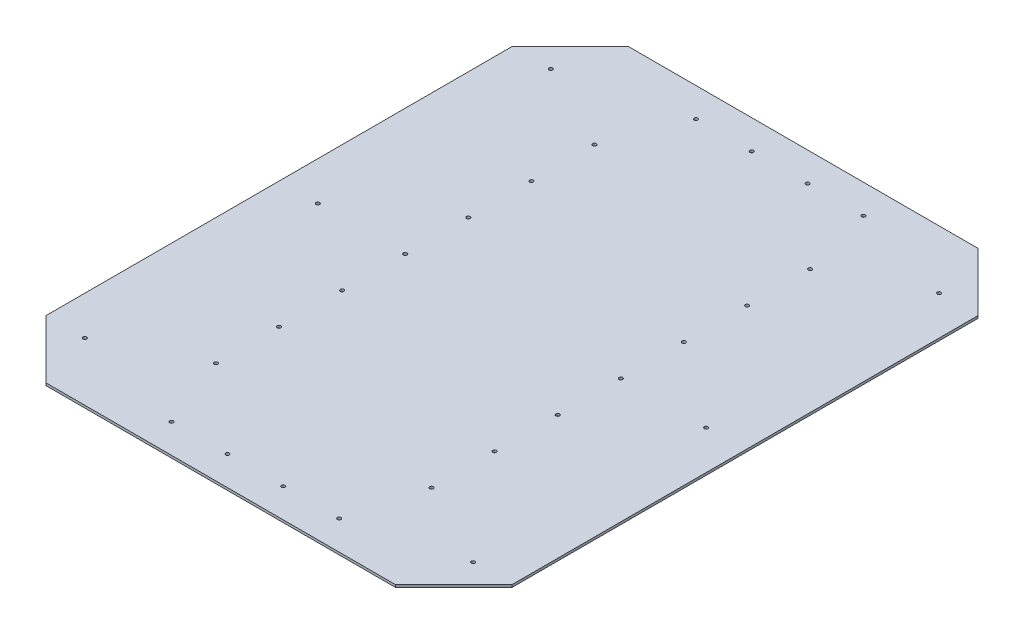
SolidWorks part; units mm, degrees
material "AISI 1010 Steel, hot rolled bar"
ref_plane "Front Plane" through (0, 0, 0) normal (0, 0, 1) x (1, 0, 0)
ref_plane "Top Plane" through (0, 0, 0) normal (0, 1, 0) x (1, 0, 0)
ref_plane "Right Plane" through (0, 0, 0) normal (1, 0, 0) x (0, 0, -1)
sketch "Sketch1" plane through (0, 0, 0) normal (0, 1, 0) x (1, 0, 0)
  line L1 (-609.6, 762) -> (609.6, 762)
  line L2 (-609.6, 762) -> (-609.6, -762)
  line L3 (-609.6, -762) -> (609.6, -762)
  line L4 (609.6, 762) -> (609.6, -762)
  line L5 (-609.6, 762) -> (609.6, -762) construction
  line L6 (-609.6, -762) -> (609.6, 762) construction
  point P0 (0, 0)
  dimension "D1" = 1219.2
  dimension "D2" = 1524
extrude "Boss-Extrude1" add sketch "Sketch1" along normal blind 6.35
sketch "Sketch2" plane through (0, 0, 0) normal (0, -1, 0) x (1, 0, 0)
  line L0 (-609.6, 762) -> (-609.6, 685.8) construction
  line L1 (-609.6, 762) -> (609.6, 762) construction
  line L2 (-609.6, -762) -> (-609.6, 762) construction
  line L3 (-609.6, -762) -> (-609.6, -685.8) construction
  line L4 (-609.6, -685.8) -> (609.6, -685.8) construction
  line L5 (609.6, 762) -> (609.6, -762) construction
  line L6 (-609.6, 685.8) -> (609.6, 685.8) construction
  line L7 (-609.6, 0) -> (609.6, 0) construction
  dimension "D1" = 76.2
sketch "Sketch12" plane through (-609.6, 0, 0) normal (-1, 0, 0) x (0, 0, 1)
  line L0 (-533.4, 0) -> (-533.4, -50.8)
  line L1 (-762, 0) -> (-685.8, 0) construction
  line L2 (533.4, 0) -> (533.4, -50.8)
  line L3 (762, 0) -> (685.8, 0) construction
  line L4 (0, 0) -> (0, -50.8)
  line L5 (-762, 0) -> (762, 0) construction
  dimension "D1" = 50.8
  dimension "D2" = 50.8
ref_plane "Plane2" through (0, -50.8, 0) normal (0, -1, 0) x (-1, 0, 0)
sketch "Sketch14" plane through (0, -50.8, 0) normal (0, -1, 0) x (-1, 0, 0)
  line L0 (609.6, 685.8) -> (-609.6, 685.8) construction
  line L1 (609.6, -685.8) -> (-609.6, -685.8) construction
  line L2 (609.6, 685.8) -> (-609.6, 685.8)
  line L3 (609.6, -685.8) -> (-609.6, -685.8)
  line L4 (609.6, 0) -> (-609.6, 0)
sketch "Sketch20" plane through (0, 6.35, 0) normal (0, 1, 0) x (1, 0, 0)
  line L0 (0, -762) -> (0, 762) construction
  line L1 (-609.6, -762) -> (609.6, -762) construction
  line L2 (609.6, 762) -> (-609.6, 762) construction
  line L3 (-457.2, 762) -> (0, 762)
  line L4 (0, 762) -> (457.2, 762)
  line L5 (457.2, 762) -> (609.6, 609.6)
  line L6 (609.6, -762) -> (609.6, 762) construction
  line L7 (-457.2, 762) -> (-609.6, 609.6)
  line L8 (-609.6, 762) -> (-609.6, -762) construction
  line L9 (-609.6, 0) -> (609.6, 0) construction
  line L10 (-457.2, -762) -> (-609.6, -609.6)
  line L11 (457.2, -762) -> (609.6, -609.6)
  line L12 (0, -762) -> (457.2, -762)
  line L13 (-457.2, -762) -> (0, -762)
  line L14 (-609.6, -609.6) -> (-609.6, 609.6)
  line L15 (609.6, 609.6) -> (609.6, -609.6)
  line L16 (609.6, 609.6) -> (609.6, -609.6)
  circle A0 centre (0, 0) radius 1360.3436
  dimension "D1" = 457.2
  dimension "D2" = 45
  dimension "D3" = 45
  dimension "D4" = 45
  dimension "D5" = 457.2
extrude "Cut-Extrude-Thin2" cut sketch "Sketch20" against normal up to surface (6.35 mm away) thin contours A0 | L5 L4 L3 L7 L14 L10 L13 L12 L11 up to face at (0, 0, 0) thin type one direction wall 2.54
other "Structural Member1" [suppressed]
ref_plane "Plane3" through (-609.6, -50.8, -685.8) normal (1, 0, 0) x (0, -1, 0)
sketch "Sketch13" plane through (-609.6, -50.8, -685.8) normal (1, 0, 0) x (0, -1, 0)
  line L0 (-44.45, -69.85) -> (-44.45, 69.85)
  line L1 (44.45, 69.85) -> (-44.45, 69.85)
  line L2 (44.45, 69.85) -> (44.45, -69.85)
  line L3 (-44.45, -69.85) -> (44.45, -69.85)
  line L4 (-50.8, -76.2) -> (50.8, -76.2)
  line L5 (-50.8, -76.2) -> (-50.8, 76.2)
  line L6 (50.8, 76.2) -> (-50.8, 76.2)
  line L7 (50.8, 76.2) -> (50.8, -76.2)
  line L8 (0, 76.2) -> (0, 69.85) construction
  line L9 (0, 69.85) -> (0, -69.85) construction
  line L10 (0, -69.85) -> (0, -76.2) construction
  line L11 (50.8, 0) -> (44.45, 0) construction
  line L12 (44.45, 0) -> (-44.45, 0) construction
  line L13 (-44.45, 0) -> (-50.8, 0) construction
  point P16 (0, 0)
  dimension "Thickness" = 6.35
  dimension "V_leg" = 152.4
  dimension "H_leg" = 101.6
sketch "Sketch16" [suppressed] plane through (0, -101.6, 0) normal (0, -1, 0) x (1, 0, 0)
  line L0 (-762, 0) -> (-685.8, 0) construction
  line L1 (-762, 76.2) -> (-762, -76.2) construction
  line L2 (-762, 762) -> (-762, 609.6) construction
  line L3 (-762, 685.8) -> (-685.8, 685.8) construction
  line L4 (-762, -685.8) -> (-685.8, -685.8) construction
  line L5 (-762, -609.6) -> (-762, -762) construction
  line L6 (762, -685.8) -> (685.8, -685.8) construction
  line L7 (762, -609.6) -> (762, -762) construction
  line L8 (762, 0) -> (685.8, 0) construction
  line L9 (762, 76.2) -> (762, -76.2) construction
  line L10 (762, 685.8) -> (685.8, 685.8) construction
  line L11 (762, 762) -> (762, 609.6) construction
  line L12 (762, 685.8) -> (-762, 685.8) construction
  line L13 (762, -685.8) -> (-762, -685.8) construction
  line L14 (0, -685.8) -> (0, -609.6) construction
  line L15 (762, -609.6) -> (-762, -609.6) construction
  line L16 (0, 685.8) -> (0, 762) construction
  line L17 (762, 762) -> (-762, 762) construction
  circle A0 centre (685.8, 685.8) radius 12.7
  circle A1 centre (685.8, 0) radius 12.7
  circle A2 centre (685.8, -685.8) radius 12.7
  circle A3 centre (-685.8, -685.8) radius 12.7
  circle A4 centre (-685.8, 0) radius 12.7
  circle A5 centre (-685.8, 685.8) radius 12.7
  circle A6 centre (0, 685.8) radius 12.7
  circle A7 centre (0, -685.8) radius 12.7
  dimension "D2" = 25.4
  dimension "D1" = 76.2
extrude "Cut-Extrude1" [suppressed] cut sketch "Sketch16" against normal blind 6.35
sketch "Sketch17" [suppressed] plane through (0, 0, -762) normal (0, 0, -1) x (-1, 0, 0)
  line L0 (-762, -50.8) -> (762, -50.8) construction
  line L1 (-762, -101.6) -> (-762, 0) construction
  line L2 (762, -101.6) -> (762, 0) construction
  circle A0 centre (0, -50.8) radius 31.75
  dimension "D1" = 63.5
extrude "Cut-Extrude2" [suppressed] cut sketch "Sketch17" against normal blind 6.35
sketch "Sketch18" [suppressed] plane through (0, 0, 762) normal (0, 0, 1) x (1, 0, 0)
  circle A1 centre (0, -50.8) radius 31.75
  circle A2 centre (0, -50.8) radius 31.75
  dimension "D1" = 0
extrude "Cut-Extrude3" [suppressed] cut sketch "Sketch18" against normal blind 6.35
sketch "Sketch21" [suppressed] plane through (0, -101.6, 0) normal (0, -1, 0) x (1, 0, 0)
  line L0 (-762, 0) -> (-685.8, 0) construction
  line L1 (-762, 76.2) -> (-762, -76.2) construction
  line L2 (762, 0) -> (685.8, 0) construction
  line L3 (762, 76.2) -> (762, -76.2) construction
  line L4 (457.2, 762) -> (457.2, 609.6) construction
  line L5 (609.6, 609.6) -> (-330.2, 609.6) construction
  line L6 (-177.8, 762) -> (-177.8, 609.6) construction
  line L7 (-177.8, -762) -> (-177.8, -609.6) construction
  line L8 (609.6, -609.6) -> (-330.2, -609.6) construction
  line L9 (457.2, -762) -> (457.2, -609.6) construction
  line L10 (-177.8, -685.8) -> (-101.6, -685.8) construction
  line L11 (457.2, -685.8) -> (381, -685.8) construction
  line L12 (457.2, 685.8) -> (381, 685.8) construction
  line L13 (-177.8, 685.8) -> (-101.6, 685.8) construction
  circle A0 centre (381, -685.8) radius 12.7
  circle A1 centre (-101.6, -685.8) radius 12.7
  circle A2 centre (-685.8, 0) radius 12.7
  circle A3 centre (685.8, 0) radius 12.7
  circle A4 centre (381, 685.8) radius 12.7
  circle A5 centre (-101.6, 685.8) radius 12.7
  dimension "D2" = 25.4
  dimension "D1" = 76.2
extrude "Cut-Extrude4" [suppressed] cut sketch "Sketch21" against normal up to next
sketch "Sketch22" [suppressed] plane through (0, 0, 0) normal (0, -1, 0) x (1, 0, 0)
  line L0 (457.2, 762) -> (457.2, 596.5164)
  line L1 (457.2, 596.5164) -> (622.6836, 596.5164)
  line L2 (457.2, 762) -> (609.6, 609.6) construction
  line L3 (-177.8, 762) -> (457.2, 762)
  line L4 (-343.2836, 596.5164) -> (-177.8, 596.5164)
  line L5 (-609.6, 330.2) -> (-177.8, 762) construction
  line L6 (-177.8, 596.5164) -> (-177.8, 762)
  line L7 (457.2, -762) -> (457.2, -581.9092)
  line L8 (457.2, -581.9092) -> (637.2908, -581.9092)
  line L9 (609.6, -609.6) -> (457.2, -762) construction
  line L10 (-343.2836, 596.5164) -> (-609.6, 330.2)
  line L11 (-177.8, -762) -> (-177.8, -585.441)
  line L12 (-177.8, -585.441) -> (-354.359, -585.441)
  line L13 (-177.8, -762) -> (-609.6, -330.2) construction
  line L14 (-609.6, 0) -> (609.6, 0) construction
  line L15 (-177.8, -762) -> (457.2, -762)
  line L16 (-609.6, 330.2) -> (-609.6, -330.2)
  line L17 (-609.6, -330.2) -> (-354.359, -585.441)
  line L18 (637.2908, -581.9092) -> (609.6, -609.6)
  line L19 (609.6, -609.6) -> (609.6, 609.6)
  line L20 (609.6, 609.6) -> (622.6836, 596.5164)
  circle A0 centre (153.8634, 0) radius 1346.4673
  line M5 (457.2, -762) -> (609.6, -609.6)
  line M6 (609.6, -609.6) -> (609.6, 609.6)
  line M7 (609.6, 609.6) -> (457.2, 762)
  line M8 (457.2, 762) -> (-177.8, 762)
  line M9 (-177.8, 762) -> (-609.6, 330.2)
  line M10 (-609.6, 330.2) -> (-609.6, -330.2)
  line M11 (-609.6, -330.2) -> (-177.8, -762)
  line M12 (-177.8, -762) -> (457.2, -762)
extrude "Cut-Extrude10" [suppressed] cut sketch "Sketch22" along normal through all contours L12 L11 L7 L8 L1 L0 L6 L4 M12 M5 M6 M7 M8 M9 M10 M11 | A0
sketch "Sketch24" plane through (0, 0, 0) normal (0, -1, 0) x (1, 0, 0)
  circle A1 centre (-279.4, -0.0018) radius 4.7625
  circle A2 centre (-279.4, -0.0018) radius 4.7625
  circle A3 centre (-279.4, 165.0982) radius 4.7625
  circle A4 centre (-279.4, 165.0982) radius 4.7625
  circle A5 centre (-279.4, 330.1982) radius 4.7625
  circle A6 centre (-279.4, 330.1982) radius 4.7625
  circle A7 centre (-279.4, 495.2982) radius 4.7625
  circle A8 centre (-279.4, 495.2982) radius 4.7625
  circle A9 centre (87.4368, 685.8) radius 4.7625
  circle A10 centre (87.4368, 685.8) radius 4.7625
  circle A11 centre (233.4868, 685.8) radius 4.7625
  circle A12 centre (233.4868, 685.8) radius 4.7625
  circle A13 centre (284.7097, 495.2982) radius 4.7625
  circle A14 centre (284.7097, 495.2982) radius 4.7625
  circle A15 centre (284.7097, 330.1982) radius 4.7625
  circle A16 centre (284.7097, 330.1982) radius 4.7625
  circle A17 centre (284.7097, 165.0982) radius 4.7625
  circle A18 centre (284.7097, 165.0982) radius 4.7625
  circle A19 centre (284.7097, -0.0018) radius 4.7625
  circle A20 centre (284.7097, -0.0018) radius 4.7625
  circle A21 centre (284.7097, -165.1018) radius 4.7625
  circle A22 centre (284.7097, -165.1018) radius 4.7625
  circle A23 centre (284.7097, -330.2018) radius 4.7625
  circle A24 centre (284.7097, -330.2018) radius 4.7625
  circle A25 centre (284.7097, -495.3018) radius 4.7625
  circle A26 centre (284.7097, -495.3018) radius 4.7625
  circle A27 centre (233.4868, -685.8) radius 4.7625
  circle A28 centre (233.4868, -685.8) radius 4.7625
  circle A29 centre (87.4368, -685.8) radius 4.7625
  circle A30 centre (87.4368, -685.8) radius 4.7625
  circle A31 centre (-58.6132, -685.8) radius 4.7625
  circle A32 centre (-58.6132, -685.8) radius 4.7625
  circle A33 centre (-204.6632, -685.8) radius 4.7625
  circle A34 centre (-204.6632, -685.8) radius 4.7625
  circle A35 centre (-279.4, -495.3018) radius 4.7625
  circle A36 centre (-279.4, -495.3018) radius 4.7625
  circle A37 centre (-279.4, -330.2018) radius 4.7625
  circle A38 centre (-279.4, -330.2018) radius 4.7625
  circle A39 centre (-279.4, -165.1018) radius 4.7625
  circle A40 centre (-279.4, -165.1018) radius 4.7625
  circle A41 centre (508, -609.6) radius 4.7625
  circle A42 centre (508, -609.6) radius 4.7625
  circle A43 centre (508, 609.6) radius 4.7625
  circle A44 centre (508, 609.6) radius 4.7625
  circle A45 centre (-508, -609.6) radius 4.7625
  circle A46 centre (-508, -609.6) radius 4.7625
  circle A47 centre (-508, 609.6) radius 4.7625
  circle A48 centre (-508, 609.6) radius 4.7625
  circle A49 centre (-204.6632, 685.8) radius 4.7625
  circle A50 centre (-204.6632, 685.8) radius 4.7625
  circle A51 centre (-58.6132, 685.8) radius 4.7625
  circle A52 centre (-58.6132, 685.8) radius 4.7625
  circle A53 centre (-508, 0) radius 4.7625
  circle A54 centre (-508, 0) radius 4.7625
  circle A55 centre (508, 0) radius 4.7625
  circle A56 centre (508, 0) radius 4.7625
  dimension "D1" = 0
  dimension "D2" = 0
  dimension "D3" = 0
  dimension "D4" = 0
  dimension "D5" = 0
  dimension "D6" = 0
  dimension "D7" = 0
  dimension "D8" = 0
  dimension "D9" = 0
  dimension "D10" = 0
  dimension "D11" = 0
  dimension "D12" = 0
  dimension "D13" = 0
  dimension "D14" = 0
  dimension "D15" = 0
  dimension "D16" = 0
  dimension "D17" = 0
  dimension "D18" = 0
  dimension "D19" = 0
  dimension "D20" = 0
  dimension "D21" = 0
  dimension "D22" = 0
  dimension "D23" = 0
  dimension "D24" = 0
  dimension "D25" = 0
  dimension "D26" = 0
  dimension "D27" = 0
  dimension "D28" = 0
extrude "Cut-Extrude13" cut sketch "Sketch24" against normal through all
